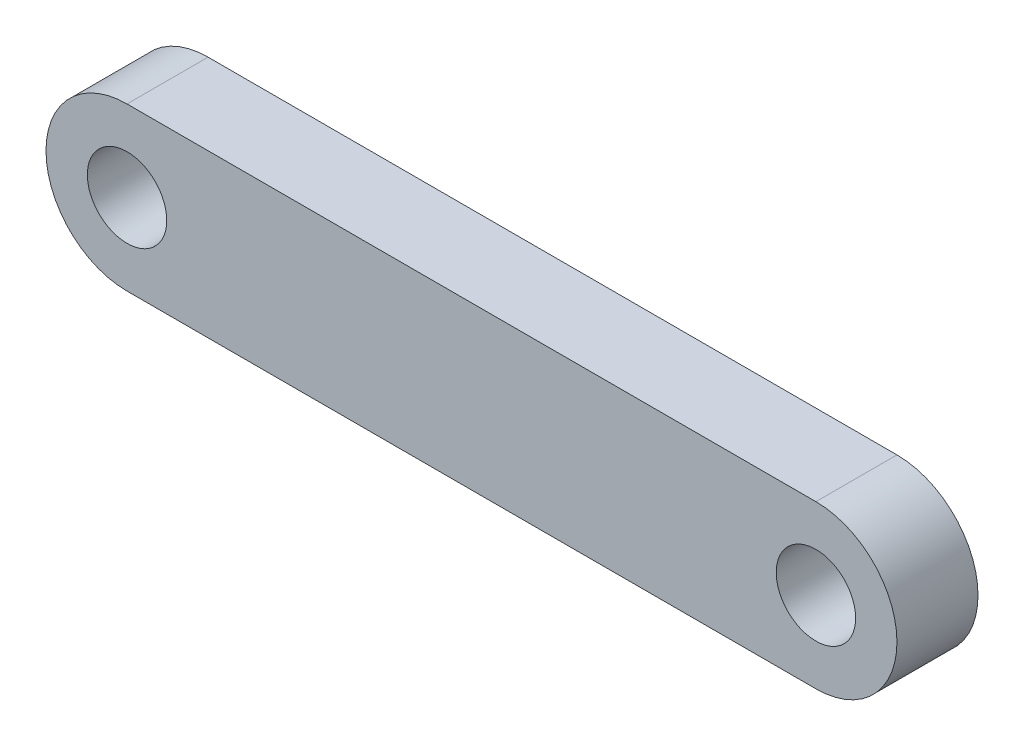
SolidWorks part; units mm, degrees
ref_plane "Front Plane" through (0, 0, 0) normal (0, 0, 1) x (1, 0, 0)
ref_plane "Top Plane" through (0, 0, 0) normal (0, 1, 0) x (1, 0, 0)
ref_plane "Right Plane" through (0, 0, 0) normal (1, 0, 0) x (0, 0, -1)
sketch "Sketch2" plane through (0, 0, 0) normal (0, 0, 1) x (1, 0, 0)
  line L0 (-26.9875, 0) -> (26.9875, 0) construction
  line L1 (-26.9875, 0) -> (26.9875, 0) construction
  line L2 (-26.9875, 6.35) -> (26.9875, 6.35)
  line L3 (-26.9875, -6.35) -> (26.9875, -6.35)
  circle A0 centre (-26.9875, 0) radius 3.1115
  circle A1 centre (26.9875, 0) radius 3.1115
  arc A2 (-26.9875, 6.35) -> (-26.9875, -6.35) centre (-26.9875, 0) ccw
  arc A3 (26.9875, -6.35) -> (26.9875, 6.35) centre (26.9875, 0) ccw
  point P3 (0, 0)
  point P4 (0, 0)
  dimension "D1" = 6.223
  dimension "D2" = 53.975
  dimension "D3" = 12.7
extrude "Boss-Extrude1" add sketch "Sketch2" along normal mid plane 6.35
